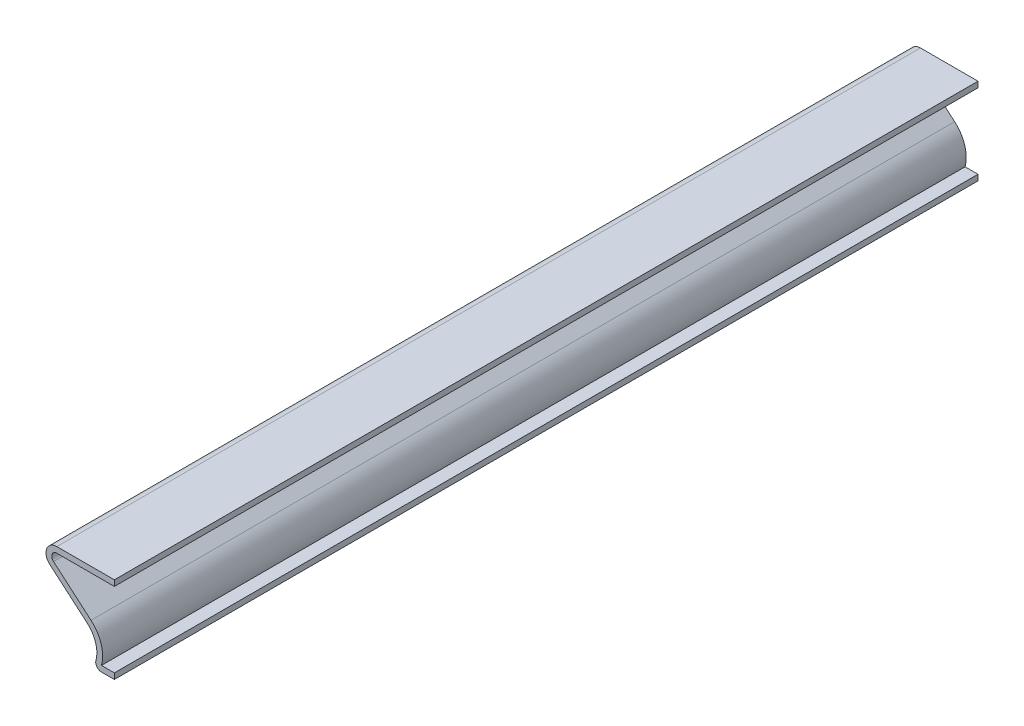
SolidWorks part; units mm, degrees
ref_plane "Front Plane" through (0, 0, 0) normal (0, 0, 1) x (1, 0, 0)
ref_plane "Top Plane" through (0, 0, 0) normal (0, 1, 0) x (1, 0, 0)
ref_plane "Right Plane" through (0, 0, 0) normal (1, 0, 0) x (0, 0, -1)
sketch "Sketch2" plane through (0, 0, 0) normal (0, 0, 1) x (1, 0, 0)
  line L0 (0, 0) -> (0, 19.05) construction
  line L1 (0, 19.05) -> (-12.7, 19.05)
  line L2 (-14.2494, 14.8605) -> (-5.9802, 7.7753)
  line L3 (-4.7625, 0) -> (0, 0)
  arc A0 (-12.7, 19.05) -> (-14.2494, 14.8605) centre (-12.7, 16.6687) ccw
  arc A1 (-5.9802, 7.7753) -> (-4.7625, 0) centre (-9.9219, 3.175) cw
  point P9 (-4.7625, 0)
  point P10 (-5.1413, 4.4919)
  point P11 (-13.8545, 14.504)
  point P12 (-3.5719, 4.8166)
  point P13 (0, 0)
  point P14 (-3.9507, 8.5509)
  point P15 (-3.8966, 5.3578)
  point P16 (-6.2778, 8.6591)
  point P18 (-5.3037, 4.7625)
  point P19 (-3.9316, 4.0247)
  point P20 (-14.4532, 15.0574)
  point P21 (-4.1717, 4.003)
  point P22 (-5.4661, 9.525)
  point P23 (-5.1955, 7.252)
  point P24 (-5.8977, 6.7518)
  dimension "D4" = 4.7625
  dimension "D1" = 19.05
  dimension "D2" = 4.7625
  dimension "D3" = 10.3187
  dimension "D5" = 5.1594
  dimension "D6" = 3.175
extrude "Extrude-Thin1" add sketch "Sketch2" against normal blind 190.5 thin thin type one direction reverse wall 1.27
fillet "Fillet1" radius 1.27 1 edges at (-4.7625, 0, -95.25)
